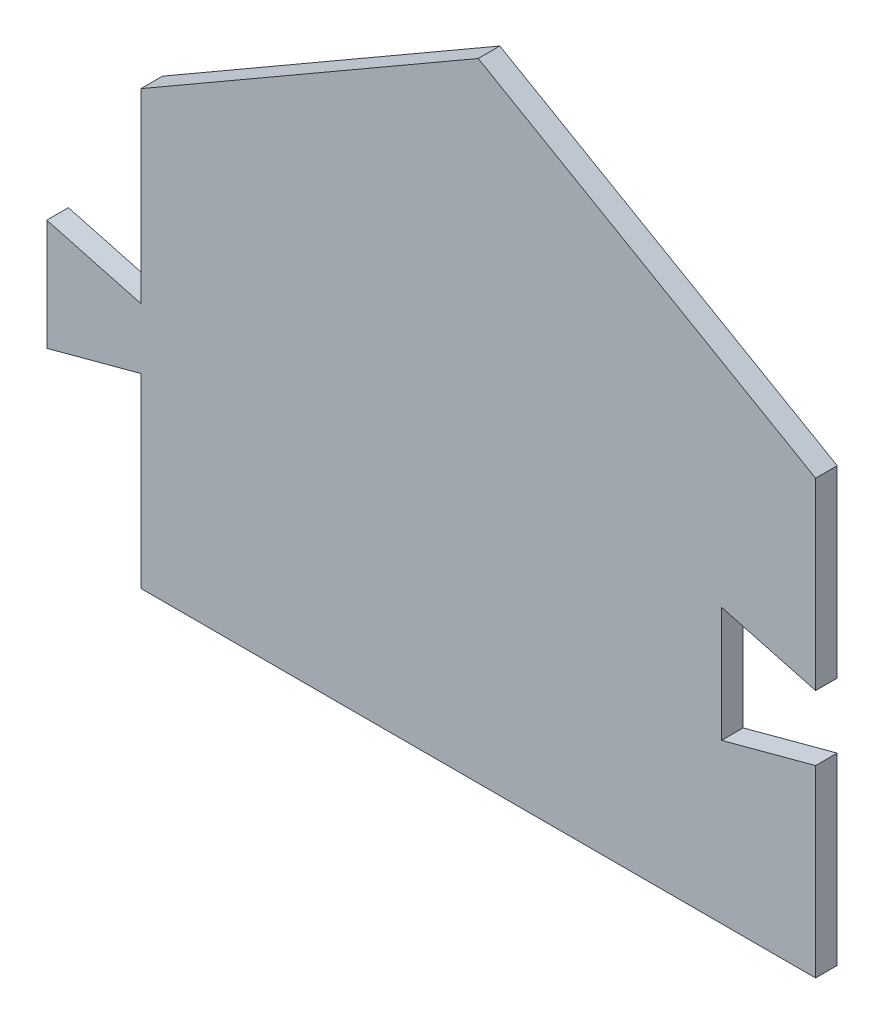
SolidWorks part; units mm, degrees
ref_plane "Front Plane" through (0, 0, 0) normal (0, 0, 1) x (1, 0, 0)
ref_plane "Top Plane" through (0, 0, 0) normal (0, 1, 0) x (1, 0, 0)
ref_plane "Right Plane" through (0, 0, 0) normal (1, 0, 0) x (0, 0, -1)
sketch "Sketch1" plane through (0, 0, 0) normal (0, 0, 1) x (1, 0, 0)
  line L0 (0, 0) -> (79.1894, 0)
  line L1 (79.1894, 0) -> (79.1894, 21.59)
  line L2 (79.1894, 21.59) -> (68.1488, 18.6317)
  line L3 (68.1488, 18.6317) -> (68.1488, 32.1683)
  line L4 (68.1488, 32.1683) -> (79.1894, 29.21)
  line L5 (79.1894, 29.21) -> (79.1894, 50.8)
  line L6 (79.1894, 50.8) -> (39.5947, 73.66)
  line L7 (39.5947, 73.66) -> (0, 50.8)
  line L8 (0, 50.8) -> (0, 28.956)
  line L12 (0, 21.844) -> (0, 0)
  line L13 (0, 28.956) -> (-11.0405, 31.9143)
  line L14 (-11.0405, 31.9143) -> (-11.0405, 18.8857)
  line L15 (-11.0405, 18.8857) -> (0, 21.844)
  dimension "D1" = 45.72
  dimension "D2" = 45.72
  dimension "D3" = 50.8
  dimension "D4" = 30
  dimension "D5" = 75
  dimension "D6" = 75
  dimension "D7" = 21.59
  dimension "D8" = 21.59
  dimension "D9" = 11.43
  dimension "D10" = 11.43
  dimension "D11" = 21.844
  dimension "D12" = 21.844
  dimension "D13" = 50.8
  dimension "D14" = 75
  dimension "D15" = 75
  dimension "D16" = 11.43
extrude "Boss-Extrude1" add sketch "Sketch1" along normal blind 2.54
